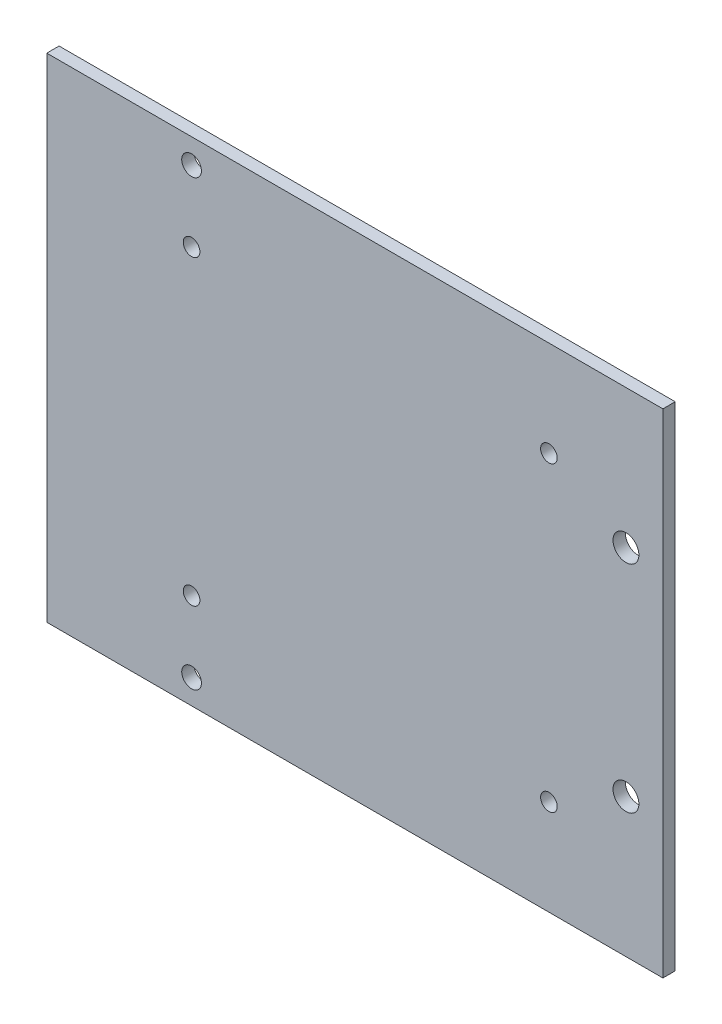
SolidWorks part; units mm, degrees
ref_plane "前视基准面" through (0, 0, 0) normal (0, 0, 1) x (1, 0, 0)
ref_plane "上视基准面" through (0, 0, 0) normal (0, 1, 0) x (1, 0, 0)
ref_plane "右视基准面" through (0, 0, 0) normal (1, 0, 0) x (0, 0, -1)
sketch "草图1" plane through (0, 0, 0) normal (0, 0, 1) x (1, 0, 0)
  line L1 (-50, 40) -> (50, 40)
  line L2 (-50, 40) -> (-50, -40)
  line L3 (-50, -40) -> (50, -40)
  line L4 (50, 40) -> (50, -40)
  line L5 (-50, 40) -> (50, -40) construction
  line L6 (-50, -40) -> (50, 40) construction
  point P0 (0, 0)
  dimension "D1" = 80
  dimension "D2" = 100
extrude "凸台-拉伸1" add sketch "草图1" along normal blind 2
sketch "草图3" plane through (0, 0, 2) normal (0, 0, 1) x (1, 0, 0)
  line L0 (-50, 0) -> (50, 0) construction
  line L1 (-26.5, -40) -> (-26.5, 40) construction
  line L2 (2.5, -40) -> (2.5, 40) construction
  line L4 (50, -40) -> (50, 40)
  line L5 (50, 40) -> (-50, 40)
  line L6 (-50, 40) -> (-50, -40)
  line L7 (-50, -40) -> (50, -40)
  line L8 (50, -40) -> (50, 40)
  line L9 (50, 40) -> (-50, 40)
  line L10 (-50, 40) -> (-50, -40)
  line L11 (-50, -40) -> (50, -40)
  circle A0 centre (-26.5, -24.5) radius 1.35
  circle A1 centre (-26.5, 24.5) radius 1.35
  circle A2 centre (31.5, 24.5) radius 1.35
  circle A3 centre (31.5, -24.5) radius 1.35
  dimension "D3" = 2.7
  dimension "D4" = 49
  dimension "D5" = 58
  dimension "D2" = 23.5
  dimension "D1" = 0
extrude "切除-拉伸1" cut sketch "草图3" against normal through all contours A0 | A1 | A2 | A3
sketch "草图4" plane through (0, 0, 0) normal (0, 0, -1) x (-1, 0, 0)
  circle A0 centre (26.5, -36) radius 1.6 construction
  circle A1 centre (26.5, -36) radius 1.6
extrude "切除-拉伸2" cut sketch "草图4" against normal through all
sketch "草图5" plane through (0, 0, 2) normal (0, 0, 1) x (1, 0, 0)
  line L0 (-26.5, 23.15) -> (-26.5, 40) construction
  line L4 (50, -40) -> (50, 40)
  line L5 (50, 40) -> (-50, 40)
  line L6 (-50, 40) -> (-50, -40)
  line L7 (-50, -40) -> (50, -40)
  line L8 (50, -40) -> (50, 40)
  line L9 (50, 40) -> (-50, 40)
  line L10 (-50, 40) -> (-50, -40)
  line L11 (-50, -40) -> (50, -40)
  circle A0 centre (-26.5, 24.5) radius 1.35 construction
  circle A1 centre (-26.5, 36) radius 1.6
  dimension "D2" = 3.2
  dimension "D3" = 11.5
  dimension "D1" = 0
extrude "切除-拉伸3" cut sketch "草图5" against normal through all contours A1
sketch "草图7" plane through (0, 0, 2) normal (0, 0, 1) x (1, 0, 0)
  line L0 (50, 0) -> (-50, 0) construction
  line L1 (44, 40) -> (44, -40) construction
  line L4 (50, -40) -> (50, 40)
  line L5 (50, 40) -> (-50, 40)
  line L6 (-50, 40) -> (-50, -40)
  line L7 (-50, -40) -> (50, -40)
  line L8 (50, -40) -> (50, 40)
  line L9 (50, 40) -> (-50, 40)
  line L10 (-50, 40) -> (-50, -40)
  line L11 (-50, -40) -> (50, -40)
  circle A0 centre (44, 17.5) radius 2.1
  circle A1 centre (44, -17.5) radius 2.1
  dimension "D3" = 4.2
  dimension "D4" = 35
  dimension "D2" = 6
  dimension "D1" = 0
extrude "切除-拉伸5" cut sketch "草图7" against normal blind 10 contours A0 | A1
sketch "草图8" plane through (0, 0, 0) normal (0, 0, -1) x (-1, 0, 0)
  line L1 (50, 40) -> (20, 40)
  line L2 (50, 40) -> (50, 10)
  line L3 (50, 10) -> (20, 10)
  line L4 (20, 40) -> (20, 10)
  dimension "D1" = 30
  dimension "D2" = 30
